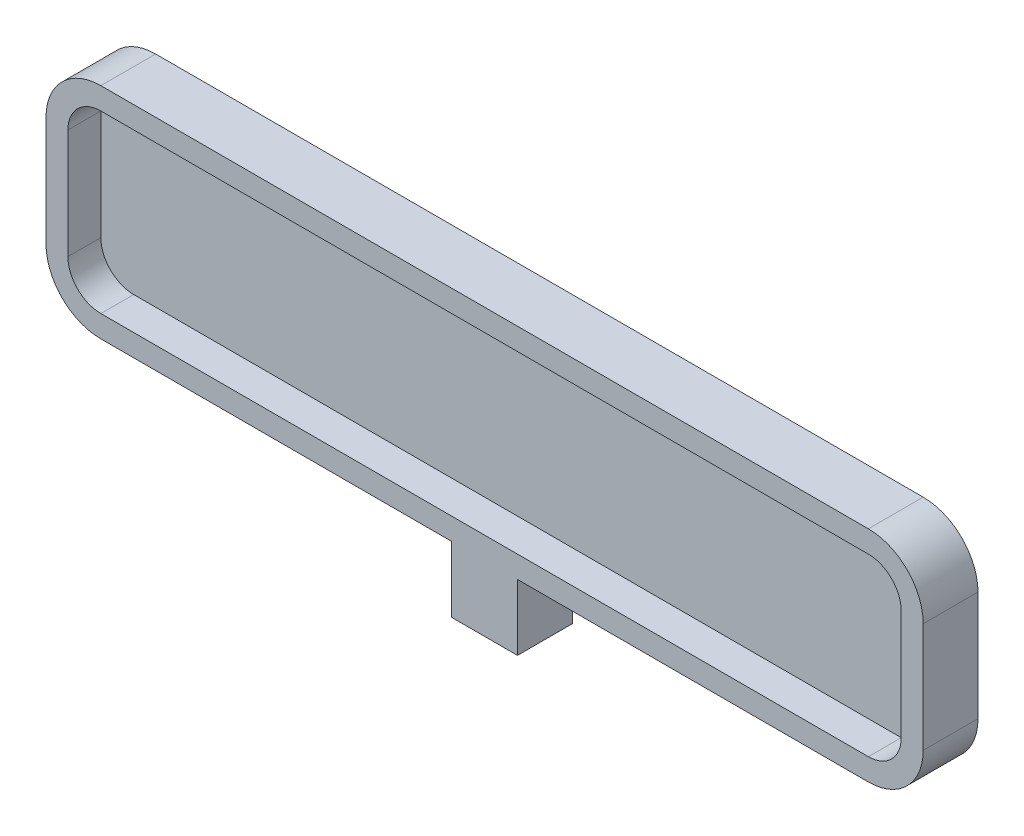
SolidWorks part; units mm, degrees
ref_plane "Front Plane" through (0, 0, 0) normal (0, 0, 1) x (1, 0, 0)
ref_plane "Top Plane" through (0, 0, 0) normal (0, 1, 0) x (1, 0, 0)
ref_plane "Right Plane" through (0, 0, 0) normal (1, 0, 0) x (0, 0, -1)
sketch "Sketch1" plane through (0, 0, 0) normal (0, 0, 1) x (1, 0, 0)
  line L1 (40, -10) -> (-40, -10)
  line L2 (40, -10) -> (40, 10)
  line L3 (40, 10) -> (-40, 10)
  line L4 (-40, -10) -> (-40, 10)
  line L5 (40, -10) -> (-40, 10) construction
  line L6 (40, 10) -> (-40, -10) construction
  point P0 (0, 0)
  dimension "D1" = 80
  dimension "D2" = 20
extrude "Boss-Extrude1" add sketch "Sketch1" along normal blind 5
fillet "Fillet1" radius 5 4 edges at (-40, -10, 2.5) (40, -10, 2.5) (40, 10, 2.5) (-40, 10, 2.5)
shell "Shell1" thickness 2
sketch "Sketch3" plane through (0, -10, 0) normal (0, -1, 0) x (1, 0, 0)
  line L0 (-35, 5) -> (35, 5) construction
  line L1 (3, 0) -> (-3, 0)
  line L2 (3, 0) -> (3, 5)
  line L3 (3, 5) -> (-3, 5)
  line L4 (-3, 0) -> (-3, 5)
  line L5 (3, 0) -> (-3, 5) construction
  line L6 (3, 5) -> (-3, 0) construction
  line L8 (-35, 0) -> (35, 0) construction
  point P9 (0, 0)
  point P11 (0, 0)
  dimension "D1" = 5
  dimension "D2" = 6
extrude "Boss-Extrude2" add sketch "Sketch3" along normal blind 6
sketch "Sketch4" plane through (0, -16, 0) normal (0, -1, 0) x (1, 0, 0)
  line L4 (-3, 0) -> (3, 0) construction
  line L5 (-3, 5) -> (-3, 0) construction
  circle A0 centre (0, 2.5) radius 2
  point P4 (0, 0)
  point P5 (0, 2.6865)
  point P8 (-3, 2.5)
  point P10 (0, 2.5847)
  dimension "D1" = 4
extrude "Cut-Extrude1" cut sketch "Sketch4" against normal blind 4
